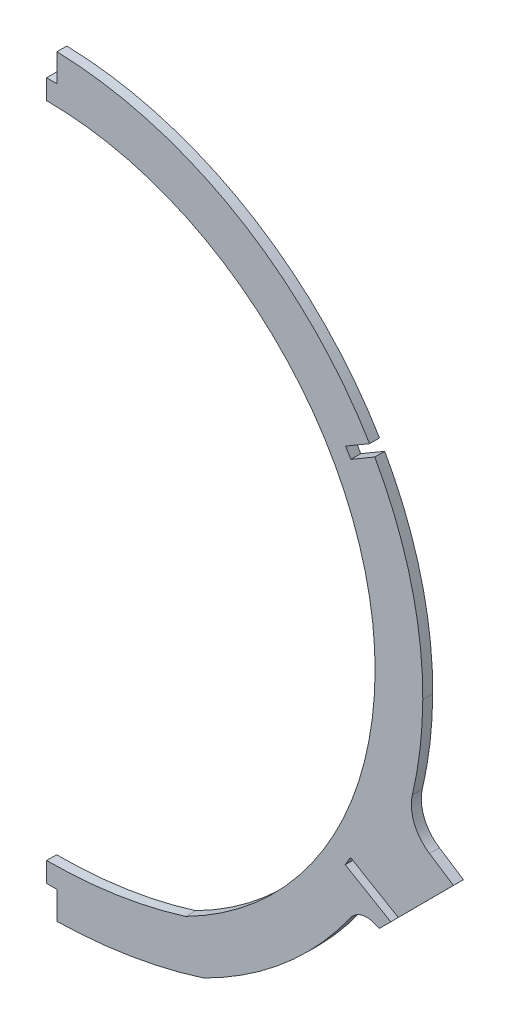
SolidWorks part; units mm, degrees
material "Plywood"
ref_plane "Front Plane" through (0, 0, 0) normal (0, 0, 1) x (1, 0, 0)
ref_plane "Top Plane" through (0, 0, 0) normal (0, 1, 0) x (1, 0, 0)
ref_plane "Right Plane" through (0, 0, 0) normal (1, 0, 0) x (0, 0, -1)
sketch "Sketch2" plane through (0, 0, 0) normal (0, 0, 1) x (1, 0, 0)
  line L0 (0, 0) -> (0.688, 245.4392) construction
  line L1 (-0.1309, -46.7153) -> (-0.2841, -101.3462) construction
  line L2 (0.0534, 19.05) -> (-169.3081, 19.05) construction
  line L3 (-72.7218, -93.726) -> (74.7111, -93.726) construction
  arc A1 (-120.0989, 19.05) -> (120.2036, 18.3433) centre (0.0534, 19.05) cw
  arc A2 (-120.0989, 19.05) -> (-50.0584, -93.726) centre (5.7147, 19.05) ccw
  arc A3 (-50.0584, -93.726) -> (50.1388, -93.726) centre (0.0402, 63.5) ccw
  arc A4 (120.2036, 18.3433) -> (50.1388, -93.726) centre (-5.6406, 19.0835) cw
  arc A5 (-104.8589, 19.05) -> (104.9639, 18.4329) centre (0.0534, 19.05) cw
  arc A6 (104.9639, 18.4329) -> (44.4049, -79.5534) centre (-5.6406, 19.0835) cw
  arc A7 (-44.324, -79.5535) -> (44.4049, -79.5534) centre (0.0402, 63.5) ccw
  arc A8 (-104.8589, 19.05) -> (-44.324, -79.5535) centre (5.7147, 19.05) ccw
  spline S0 degree 3 poles (-7457.5243, 7873.9786) (-1520.6447, 792.6716) (-232.684, -284.717) (69.4764, -82.4823) (75.8596, -77.7331) (81.7614, -72.3621) (85.2966, -68.8071) (85.996, -68.0862) (87.3792, -66.6243) (88.0639, -65.8824) (90.0847, -63.6371) (91.3894, -62.1126) (95.1787, -57.4581) (97.5389, -54.2471) (101.9343, -47.6137) (103.9694, -44.1914) (106.7765, -38.8981) (107.6712, -37.107) (109.3772, -33.4707) (110.1904, -31.6207) (112.481, -26.0415) (113.8153, -22.2742) (116.1105, -14.6467) (117.0712, -10.7866) (118.62, -2.9737) (119.208, 0.9791) (119.8028, 6.9796) (119.953, 8.9949) (120.1541, 13.0067) (120.2055, 15.0081) (120.2151, 20.9991) (119.8425, 28.9519) (118.7088, 36.835) (117.5685, 42.7208) (117.1399, 44.6783) (116.1841, 48.5842) (115.6559, 50.5346) (113.94, 56.3082) (112.6165, 60.0751) (109.6192, 67.4485) (107.9453, 71.055) (104.2453, 78.1066) (102.2192, 81.5518) (99.4588, 85.754) (98.8945, 86.5903) (97.7468, 88.2466) (97.1639, 89.0659) (95.3883, 91.4977) (94.1686, 93.0841) (90.4034, 97.7402) (87.752, 100.7072) (82.1689, 106.369) (79.2371, 109.0639) (74.6247, 112.8977) (73.0514, 114.1408) (70.6363, 115.9521) (69.821, 116.5478) (68.1799, 117.7153) (67.3537, 118.2875) (63.1947, 121.0918) (59.7778, 123.1535) (52.769, 126.9212) (49.1769, 128.6272) (41.816, 131.6806) (38.0473, 133.028) (33.2217, 134.4796) (32.2518, 134.758) (30.3116, 135.2882) (29.34, 135.5404) (26.4206, 136.2591) (24.4685, 136.6873) (18.5945, 137.8219) (14.6552, 138.3782) (6.7301, 139.0933) (2.7444, 139.252) (-2.2675, 139.1959) (-3.2714, 139.172) (-5.2821, 139.0983) (-6.2905, 139.0484) (-9.3072, 138.8606) (-11.3068, 138.6846) (-17.272, 138.0072) (-25.1357, 136.7069) (-32.823, 134.6274) (-38.5216, 132.7724) (-40.41, 132.1048) (-44.1641, 130.6694) (-46.0326, 129.9002) (-538.3584, -87.5727) (554.8292, -3549.2971) (3251.8348, -10297.372) knots -2.787439 -2.787439 -2.787439 -2.787439 0.03125 0.03125 0.0625 0.09375 0.09375 0.101563 0.101563 0.109375 0.109375 0.125 0.125 0.15625 0.15625 0.1875 0.1875 0.203125 0.203125 0.21875 0.21875 0.25 0.25 0.28125 0.28125 0.3125 0.3125 0.328125 0.328125 0.34375 0.34375 0.375 0.40625 0.40625 0.421875 0.421875 0.4375 0.4375 0.46875 0.46875 0.5 0.5 0.53125 0.53125 0.539063 0.539063 0.546875 0.546875 0.5625 0.5625 0.59375 0.59375 0.625 0.625 0.640625 0.640625 0.648438 0.648438 0.65625 0.65625 0.6875 0.6875 0.71875 0.71875 0.75 0.75 0.757813 0.757813 0.765625 0.765625 0.78125 0.78125 0.8125 0.8125 0.84375 0.84375 0.851563 0.851563 0.859375 0.859375 0.875 0.875 0.90625 0.9375 0.9375 0.953125 0.953125 0.96875 0.96875 5.126469 5.126469 5.126469 5.126469 only from (55.8537, -90.8749) to (-58.6671, 123.6507)
  spline S1 degree 3 poles (55.8537, -90.8749) (59.4151, -88.9779) (62.8499, -86.9173) (69.4764, -82.4823) (75.8596, -77.7331) (81.7614, -72.3621) (85.2966, -68.8071) (85.996, -68.0862) (87.3792, -66.6243) (88.0639, -65.8824) (90.0847, -63.6371) (91.3894, -62.1126) (95.1787, -57.4581) (97.5389, -54.2471) (101.9343, -47.6137) (103.9694, -44.1914) (106.7765, -38.8981) (107.6712, -37.107) (109.3772, -33.4707) (110.1904, -31.6207) (112.481, -26.0415) (113.8153, -22.2742) (116.1105, -14.6467) (117.0712, -10.7866) (118.62, -2.9737) (119.208, 0.9791) (119.8028, 6.9796) (119.953, 8.9949) (120.1541, 13.0067) (120.2055, 15.0081) (120.2151, 20.9991) (119.8425, 28.9519) (118.7088, 36.835) (117.5685, 42.7208) (117.1399, 44.6783) (116.1841, 48.5842) (115.6559, 50.5346) (113.94, 56.3082) (112.6165, 60.0751) (109.6192, 67.4485) (107.9453, 71.055) (104.2453, 78.1066) (102.2192, 81.5518) (99.4588, 85.754) (98.8945, 86.5903) (97.7468, 88.2466) (97.1639, 89.0659) (95.3883, 91.4977) (94.1686, 93.0841) (90.4034, 97.7402) (87.752, 100.7072) (82.1689, 106.369) (79.2371, 109.0639) (74.6247, 112.8977) (73.0514, 114.1408) (70.6363, 115.9521) (69.821, 116.5478) (68.1799, 117.7153) (67.3537, 118.2875) (63.1947, 121.0918) (59.7778, 123.1535) (52.769, 126.9212) (49.1769, 128.6272) (41.816, 131.6806) (38.0473, 133.028) (33.2217, 134.4796) (32.2518, 134.758) (30.3116, 135.2882) (29.34, 135.5404) (26.4206, 136.2591) (24.4685, 136.6873) (18.5945, 137.8219) (14.6552, 138.3782) (6.7301, 139.0933) (2.7444, 139.252) (-2.2675, 139.1959) (-3.2714, 139.172) (-5.2821, 139.0983) (-6.2905, 139.0484) (-9.3072, 138.8606) (-11.3068, 138.6846) (-17.272, 138.0072) (-25.1357, 136.7069) (-32.823, 134.6274) (-38.5216, 132.7724) (-40.41, 132.1048) (-44.1641, 130.6694) (-46.0326, 129.9002) (-51.5624, 127.4576) (-55.1595, 125.6458) (-58.6671, 123.6507) knots 0 0 0 0 0.03125 0.03125 0.0625 0.09375 0.09375 0.101563 0.101563 0.109375 0.109375 0.125 0.125 0.15625 0.15625 0.1875 0.1875 0.203125 0.203125 0.21875 0.21875 0.25 0.25 0.28125 0.28125 0.3125 0.3125 0.328125 0.328125 0.34375 0.34375 0.375 0.40625 0.40625 0.421875 0.421875 0.4375 0.4375 0.46875 0.46875 0.5 0.5 0.53125 0.53125 0.539063 0.539063 0.546875 0.546875 0.5625 0.5625 0.59375 0.59375 0.625 0.625 0.640625 0.640625 0.648438 0.648438 0.65625 0.65625 0.6875 0.6875 0.71875 0.71875 0.75 0.75 0.757813 0.757813 0.765625 0.765625 0.78125 0.78125 0.8125 0.8125 0.84375 0.84375 0.851563 0.851563 0.859375 0.859375 0.875 0.875 0.90625 0.9375 0.9375 0.953125 0.953125 0.96875 0.96875 1 1 1 1 construction
  spline S2 degree 3 poles (7698.4035, -7600.8615) (1611.4613, -764.0515) (222.821, 341.9355) (-76.9523, 111.0297) (-81.0984, 107.3558) (-85.9766, 102.3921) (-86.9369, 101.3807) (-88.8267, 99.3202) (-89.7577, 98.2691) (-92.4915, 95.0728) (-94.2304, 92.8907) (-99.2026, 86.1952) (-102.1931, 81.5333) (-106.1993, 74.2476) (-107.4545, 71.77) (-109.2154, 67.9791) (-109.782, 66.7031) (-110.874, 64.1258) (-111.4002, 62.8224) (-113.9097, 56.2871) (-115.5417, 50.9767) (-118.0823, 40.1978) (-118.9908, 34.7292) (-119.6657, 27.7928) (-119.7775, 26.4005) (-119.9543, 23.6055) (-120.0192, 22.2016) (-120.1418, 18.0057) (-120.1286, 15.2199) (-119.8102, 6.8959) (-119.2278, 1.3912) (-117.8014, -6.7994) (-117.2335, -9.5184) (-116.2404, -13.58) (-115.8858, -14.9311) (-115.1288, -17.6274) (-114.7258, -18.9739) (-112.6063, -25.6411) (-108.5276, -35.9696) (-103.1136, -45.6397) (-99.3011, -51.4722) (-98.5171, -52.628) (-96.9053, -54.9182) (-96.0765, -56.0537) (-93.5433, -59.4015) (-91.7865, -61.5635) (-86.3167, -67.8444) (-82.4051, -71.759) (-76.1398, -77.2217) (-73.9848, -78.9742) (-70.6503, -81.498) (-69.5218, -82.3217) (-67.2303, -83.9337) (-66.0665, -84.7222) (591.775, -513.8293) (4465.0583, 6093.4616) (-858.1872, -7414.6277) knots -4.145324 -4.145324 -4.145324 -4.145324 0.0625 0.0625 0.125 0.125 0.140625 0.140625 0.15625 0.15625 0.1875 0.1875 0.25 0.25 0.28125 0.28125 0.296875 0.296875 0.3125 0.3125 0.375 0.375 0.4375 0.4375 0.453125 0.453125 0.46875 0.46875 0.5 0.5 0.5625 0.5625 0.59375 0.59375 0.609375 0.609375 0.625 0.625 0.6875 0.75 0.75 0.765625 0.765625 0.78125 0.78125 0.8125 0.8125 0.875 0.875 0.90625 0.90625 0.921875 0.921875 0.9375 0.9375 9.693438 9.693438 9.693438 9.693438 only from (-58.6671, 123.6507) to (-50.3455, -93.5936)
  spline S3 degree 3 poles (-6093.8521, 8949.2565) (1657.017, -4470.2733) (1699.3783, -2108.1952) (-3189.6914, 10349.9889) knots -230.213154 -230.213154 -230.213154 -230.213154 248.242551 248.242551 248.242551 248.242551 only from (49.819, -93.8744) to (55.8537, -90.8749)
  spline S4 degree 3 poles (49.819, -93.8744) (51.8584, -92.9316) (53.87, -91.9317) (55.8537, -90.8749) knots 0 0 0 0 1 1 1 1 construction
  spline S5 degree 3 poles (-58.6671, 123.6507) (-63.5487, 120.874) (-68.1774, 117.7887) (-76.9523, 111.0297) (-81.0984, 107.3558) (-85.9766, 102.3921) (-86.9369, 101.3807) (-88.8267, 99.3202) (-89.7577, 98.2691) (-92.4915, 95.0728) (-94.2304, 92.8907) (-99.2026, 86.1952) (-102.1931, 81.5333) (-106.1993, 74.2476) (-107.4545, 71.77) (-109.2154, 67.9791) (-109.782, 66.7031) (-110.874, 64.1258) (-111.4002, 62.8224) (-113.9097, 56.2871) (-115.5417, 50.9767) (-118.0823, 40.1978) (-118.9908, 34.7292) (-119.6657, 27.7928) (-119.7775, 26.4005) (-119.9543, 23.6055) (-120.0192, 22.2016) (-120.1418, 18.0057) (-120.1286, 15.2199) (-119.8102, 6.8959) (-119.2278, 1.3912) (-117.8014, -6.7994) (-117.2335, -9.5184) (-116.2404, -13.58) (-115.8858, -14.9311) (-115.1288, -17.6274) (-114.7258, -18.9739) (-112.6063, -25.6411) (-108.5276, -35.9696) (-103.1136, -45.6397) (-99.3011, -51.4722) (-98.5171, -52.628) (-96.9053, -54.9182) (-96.0765, -56.0537) (-93.5433, -59.4015) (-91.7865, -61.5635) (-86.3167, -67.8444) (-82.4051, -71.759) (-76.1398, -77.2217) (-73.9848, -78.9742) (-70.6503, -81.498) (-69.5218, -82.3217) (-67.2303, -83.9337) (-66.0665, -84.7222) (-60.2073, -88.5441) (-55.3561, -91.2432) (-50.3455, -93.5936) knots 0 0 0 0 0.0625 0.0625 0.125 0.125 0.140625 0.140625 0.15625 0.15625 0.1875 0.1875 0.25 0.25 0.28125 0.28125 0.296875 0.296875 0.3125 0.3125 0.375 0.375 0.4375 0.4375 0.453125 0.453125 0.46875 0.46875 0.5 0.5 0.5625 0.5625 0.59375 0.59375 0.609375 0.609375 0.625 0.625 0.6875 0.75 0.75 0.765625 0.765625 0.78125 0.78125 0.8125 0.8125 0.875 0.875 0.90625 0.90625 0.921875 0.921875 0.9375 0.9375 1 1 1 1 construction
  spline S6 degree 3 poles (-2482.9215, 10606.6105) (134.4304, 111.18) (111.5262, -73.4925) (45.8458, -95.3665) (44.8322, -95.6594) (41.7708, -96.4587) (39.7032, -96.8873) (35.5384, -97.6293) (33.4392, -97.9405) (29.2422, -98.4783) (27.1412, -98.7049) (20.8322, -99.2882) (16.6185, -99.55) (8.1799, -99.8877) (3.9548, -99.9623) (-4.5058, -99.9387) (-8.734, -99.8405) (-17.1695, -99.4557) (-21.3793, -99.1705) (-27.6778, -98.553) (-29.7745, -98.3152) (-33.9608, -97.7556) (-36.0504, -97.4344) (-39.177, -96.8603) (-40.2191, -96.653) (-42.292, -96.1992) (-43.3225, -95.953) (-45.3676, -95.407) (-46.3821, -95.1076) (-112.5445, -72.6554) (-128.1138, 114.0017) (2927.5642, 10491.2531) knots -1.983598 -1.983598 -1.983598 -1.983598 0.03125 0.03125 0.0625 0.0625 0.125 0.125 0.1875 0.1875 0.25 0.25 0.375 0.375 0.5 0.5 0.625 0.625 0.75 0.75 0.8125 0.8125 0.875 0.875 0.90625 0.90625 0.9375 0.9375 0.96875 0.96875 3.000363 3.000363 3.000363 3.000363 only from (49.8185, -93.8746) to (-50.3451, -93.5938)
  spline S7 degree 3 poles (49.8185, -93.8746) (48.8452, -94.325) (47.8521, -94.6984) (45.8458, -95.3665) (44.8322, -95.6594) (41.7708, -96.4587) (39.7032, -96.8873) (35.5384, -97.6293) (33.4392, -97.9405) (29.2422, -98.4783) (27.1412, -98.7049) (20.8322, -99.2882) (16.6185, -99.55) (8.1799, -99.8877) (3.9548, -99.9623) (-4.5058, -99.9387) (-8.734, -99.8405) (-17.1695, -99.4557) (-21.3793, -99.1705) (-27.6778, -98.553) (-29.7745, -98.3152) (-33.9608, -97.7556) (-36.0504, -97.4344) (-39.177, -96.8603) (-40.2191, -96.653) (-42.292, -96.1992) (-43.3225, -95.953) (-45.3676, -95.407) (-46.3821, -95.1076) (-48.3867, -94.4274) (-49.3773, -94.0483) (-50.3451, -93.5938) knots 0 0 0 0 0.03125 0.03125 0.0625 0.0625 0.125 0.125 0.1875 0.1875 0.25 0.25 0.375 0.375 0.5 0.5 0.625 0.625 0.75 0.75 0.8125 0.8125 0.875 0.875 0.90625 0.90625 0.9375 0.9375 0.96875 0.96875 1 1 1 1 construction
  spline S8 degree 1 poles (44.4895, -82.3468) (49.8828, -79.6661) knots 0 0 1 1 construction
  spline S9 degree 1 poles (49.8828, -79.6661) (-52.388, 112.6115) knots 0 0 1 1 construction
  spline S10 degree 1 poles (-52.388, 112.6115) (-44.952, -82.0958) knots 0 0 1 1 construction
  spline S11 degree 3 poles (44.4895, -82.3468) (44.9451, -82.1361) (45.8533, -81.7084) (47.2062, -81.0479) (48.5497, -80.3682) (49.4396, -79.9022) (49.8828, -79.6661) knots 0 0 0 0 0.250007 0.500014 0.750021 1.000028 1.000028 1.000028 1.000028 construction
  spline S12 degree 3 poles (49.8828, -79.6661) (51.4682, -78.8216) (54.6039, -77.0481) (60.6329, -73.2256) (67.7713, -67.9145) (75.6946, -60.7068) (85.376, -49.946) (92.2499, -39.5527) (97.0635, -29.9209) (99.9774, -23.2906) (102.9687, -14.8438) (105.5551, -4.452) (106.8747, 4.4138) (107.4138, 11.642) (107.598, 18.8242) (107.1791, 27.7507) (105.6575, 38.3493) (103.0737, 48.9109) (99.5091, 59.0529) (95.0071, 68.7524) (90.4672, 76.4728) (86.3465, 82.4205) (79.7918, 90.9419) (71.0678, 99.805) (59.5047, 108.4813) (50.3361, 114.0108) (40.7123, 118.5824) (32.2831, 121.5955) (25.3334, 123.4944) (18.366, 125.0225) (9.571, 126.2643) (-1.0997, 126.6912) (-11.9104, 126.0185) (-22.4327, 124.2743) (-36.1547, 120.5693) (-46.1487, 116.1604) (-52.388, 112.6115) knots 0 0 0 0 0.015625 0.03125 0.0625 0.09375 0.125 0.1875 0.203125 0.21875 0.25 0.28125 0.3125 0.328125 0.34375 0.375 0.40625 0.4375 0.46875 0.5 0.53125 0.546875 0.5625 0.625 0.65625 0.6875 0.71875 0.75 0.765625 0.78125 0.8125 0.84375 0.875 0.90625 0.9375 1 1 1 1 construction
  spline S13 degree 3 poles (-52.388, 112.6115) (-54.5585, 111.3769) (-58.8261, 108.7475) (-66.8816, 102.9693) (-76.1597, 94.757) (-85.9932, 83.258) (-92.681, 72.8203) (-97.1816, 63.9424) (-101.112, 54.6656) (-104.776, 42.7383) (-106.8137, 30.488) (-107.4512, 20.4245) (-107.4028, 10.4189) (-106.3564, 0.5368) (-104.3212, -9.2152) (-101.5955, -18.9231) (-97.0158, -30.5128) (-90.9605, -41.334) (-85.1677, -49.567) (-78.8706, -57.3154) (-71.8665, -64.3232) (-64.1621, -70.5906) (-57.9948, -74.9291) (-51.5954, -78.7902) (-47.193, -81.0446) (-44.952, -82.0958) knots 0 0 0 0 0.03125 0.0625 0.125 0.1875 0.25 0.28125 0.3125 0.375 0.4375 0.46875 0.5 0.5625 0.59375 0.625 0.6875 0.75 0.78125 0.8125 0.875 0.90625 0.9375 0.96875 1 1 1 1 construction
  spline S14 degree 1 poles (44.4849, -82.3489) (-44.9469, -82.0982) knots 0 0 1 1 construction
  spline S15 degree 3 poles (44.4849, -82.3489) (44.3746, -82.3999) (44.1627, -82.4934) (43.6492, -82.7012) (42.8561, -82.9839) (41.7841, -83.3184) (40.2245, -83.7477) (38.1103, -84.2445) (35.4106, -84.7656) (32.6063, -85.224) (28.7759, -85.7537) (23.885, -86.2821) (17.9201, -86.7432) (11.8971, -87.0512) (5.8396, -87.2261) (-2.2666, -87.2864) (-10.3738, -87.0974) (-18.3985, -86.6419) (-24.3556, -86.1481) (-29.2377, -85.5934) (-33.056, -85.0443) (-35.8555, -84.5718) (-38.5671, -84.0318) (-40.6899, -83.5223) (-42.2517, -83.0828) (-43.3238, -82.7417) (-44.1147, -82.4546) (-44.6269, -82.2439) (-44.8373, -82.1497) (-44.9469, -82.0982) knots 0 0 0 0 0.007812 0.015625 0.03125 0.046875 0.0625 0.09375 0.125 0.15625 0.1875 0.25 0.3125 0.375 0.4375 0.5 0.625 0.6875 0.75 0.8125 0.84375 0.875 0.90625 0.9375 0.953125 0.96875 0.984375 0.992188 1 1 1 1 construction
  point P12 (-0.2802, -99.9505)
  dimension "D3" = 19.05
  dimension "D4" = 93.726
  dimension "D5" = 63.5
  dimension "D6" = 15.24
  dimension "D1" = 12.7
  dimension "D2" = 12.7
extrude "Boss-Extrude1" add sketch "Sketch2" along normal mid plane 3.175
sketch "Sketch3" plane through (0, 0, 0) normal (1, 0, 0) x (0, 0, -1)
  line L1 (-100.0568, 212.3798) -> (108.5889, 212.3798)
  line L2 (-100.0568, 212.3798) -> (-100.0568, -170.6472)
  line L3 (-100.0568, -170.6472) -> (108.5889, -170.6472)
  line L4 (108.5889, 212.3798) -> (108.5889, -170.6472)
extrude "Cut-Extrude1" cut sketch "Sketch3" against normal through all
sketch "Sketch5" plane through (0, 0, 0) normal (0, 0, 1) x (1, 0, 0)
  line L0 (0, 0) -> (196.1994, 0) construction
  line L1 (106.2582, -51.9887) -> (130.0117, -28.1684)
  line L2 (130.0117, -28.1684) -> (114.5738, -18.1429)
  line L3 (106.2582, -51.9887) -> (100.047, -49.2352)
  line L4 (100.047, -49.2352) -> (114.5738, -18.1429)
  arc A0 (50.1388, -93.726) -> (120.2036, 18.3433) centre (-5.6406, 19.0835) ccw construction
  dimension "D1" = 33
  dimension "D2" = 18.1429
  dimension "D3" = 78.08
  dimension "D4" = 18.4076
  dimension "D6" = 33.6398
  dimension "D7" = 6.7941
extrude "Boss-Extrude2" add sketch "Sketch5" along normal mid plane 3.175
fillet "Fillet1" radius 6.35 1 edges at (100.047, -49.2352, 0)
fillet "Fillet2" radius 12.7 1 edges at (114.5738, -18.1429, 0)
sketch "Sketch6" plane through (0, 0, 1.5875) normal (0, 0, 1) x (1, 0, 0)
  line L0 (0, 0) -> (0, 123.9623) construction
  line L1 (0, 123.9623) -> (0, 130.3123) construction
  line L2 (0, 123.9623) -> (0, 139.2023) construction
  line L3 (0, 130.3123) -> (3.302, 130.3123)
  line L4 (0, 130.3123) -> (0, 143.0123)
  line L5 (3.302, 130.3123) -> (3.302, 143.0123)
  line L6 (0, 143.0123) -> (3.302, 143.0123)
  line L7 (90.9009, 71.522) -> (96.3775, 74.7361) construction
  line L11 (108.1662, 79.7402) -> (106.4949, 82.588)
  line L12 (90.9009, 71.522) -> (0, 18.1749) construction
  line L13 (108.1662, 79.7402) -> (97.2131, 73.3122)
  line L14 (106.4949, 82.588) -> (95.5418, 76.16)
  line L15 (97.2131, 73.3122) -> (95.5418, 76.16)
  line L22 (95.4243, -39.7411) -> (97.0955, -36.8933)
  line L23 (90.7834, -35.1032) -> (0, 18.1749) construction
  line L24 (95.4243, -39.7411) -> (116.4589, -52.0857)
  line L25 (97.0955, -36.8933) -> (118.1302, -49.2379)
  line L26 (116.4589, -52.0857) -> (118.1302, -49.2379)
  line L27 (90.7834, -35.1032) -> (96.2599, -38.3172) construction
  line L28 (0, 0) -> (0, -86.2748) construction
  line L29 (0, -86.2748) -> (0, -92.6248) construction
  line L31 (0, -92.6248) -> (3.302, -92.6248)
  line L32 (0, -92.6248) -> (0, -105.3248)
  line L33 (3.302, -92.6248) -> (3.302, -105.3248)
  line L34 (0, -105.3248) -> (3.302, -105.3248)
  point P4 (96.3775, 74.7361)
  point P14 (96.2599, -38.3172)
  dimension "D1" = 123.9623
  dimension "D2" = 6.35
  dimension "D3" = 3.302
  dimension "D4" = 12.7
  dimension "D5" = 18.1749
  dimension "D6" = 59.593
  dimension "D7" = 105.3987
  dimension "D8" = 6.35
  dimension "D9" = 3.302
  dimension "D10" = 12.7
  dimension "D11" = 59.593
  dimension "D12" = 105.2624
  dimension "D13" = 3.302
  dimension "D14" = 6.35
  dimension "D15" = 86.2748
  dimension "D16" = 6.35
  dimension "D17" = 3.302
  dimension "D18" = 12.7
extrude "Cut-Extrude2" cut sketch "Sketch6" against normal through all
